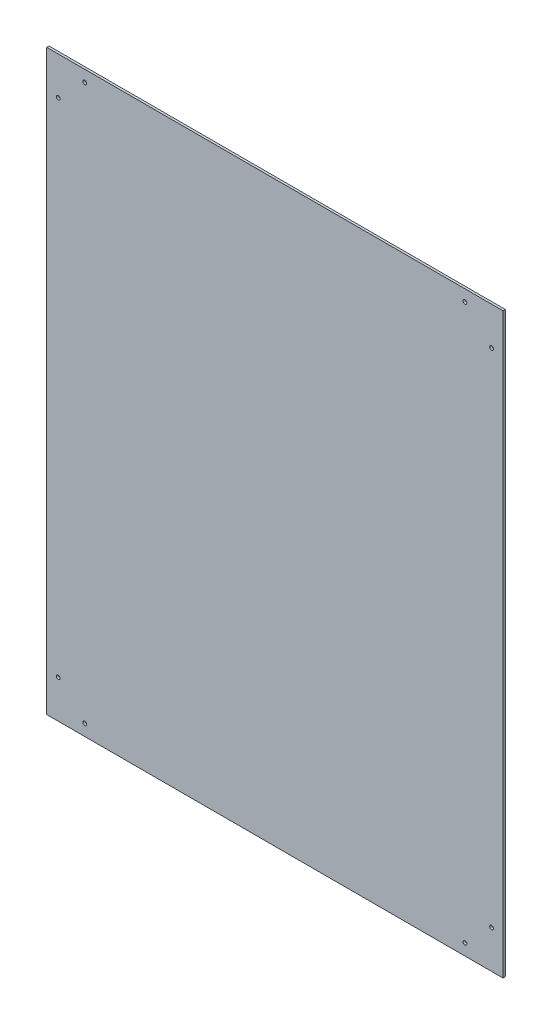
SolidWorks part; units mm, degrees
ref_plane "Plan de face" through (0, 0, 0) normal (0, 0, 1) x (1, 0, 0)
ref_plane "Plan de dessus" through (0, 0, 0) normal (0, 1, 0) x (1, 0, 0)
ref_plane "Plan de droite" through (0, 0, 0) normal (1, 0, 0) x (0, 0, -1)
sketch "Esquisse1" plane through (0, 0, 0) normal (0, 0, 1) x (1, 0, 0)
  line L1 (0, 0) -> (600, 0)
  line L2 (0, 0) -> (0, 760)
  line L3 (0, 760) -> (600, 760)
  line L4 (600, 0) -> (600, 760)
  dimension "D1" = 760
  dimension "D2" = 600
extrude "Boss.-Extru.1" add sketch "Esquisse1" along normal blind 3
sketch "Esquisse2" plane through (0, 0, 3) normal (0, 0, 1) x (1, 0, 0)
  line L0 (300, 760) -> (300, 0) construction
  line L1 (600, 760) -> (0, 760) construction
  line L2 (0, 0) -> (600, 0) construction
  line L3 (0, 760) -> (0, 0) construction
  circle A0 centre (50, 745) radius 2.5
  circle A1 centre (15, 710) radius 2.5
  circle A2 centre (15, 50) radius 2.5
  circle A3 centre (50, 15) radius 2.5
  circle A4 centre (550, 15) radius 2.5
  circle A5 centre (585, 50) radius 2.5
  circle A6 centre (585, 710) radius 2.5
  circle A7 centre (550, 745) radius 2.5
  point P18 (0, 12.9164)
  dimension "D1" = 5
  dimension "D2" = 15
  dimension "D3" = 15
  dimension "D4" = 50
  dimension "D5" = 50
  dimension "D6" = 15
  dimension "D7" = 50
  dimension "D8" = 50
  dimension "D9" = 15
extrude "Enlèv. mat.-Extru.1" cut sketch "Esquisse2" against normal blind 3
